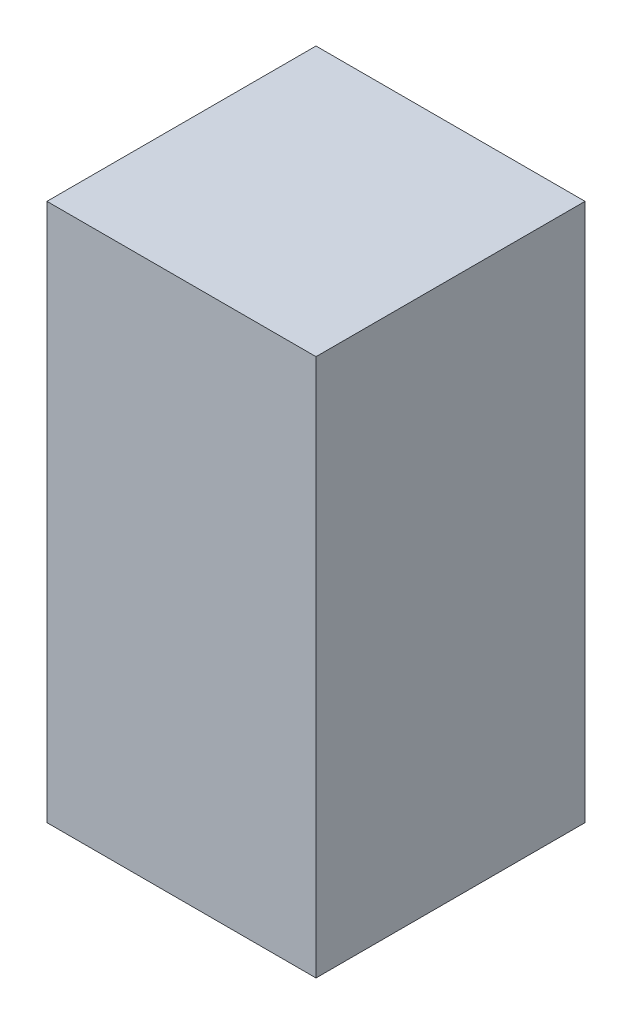
SolidWorks part; units mm, degrees
ref_plane "Front Plane" through (0, 0, 0) normal (0, 0, 1) x (1, 0, 0)
ref_plane "Top Plane" through (0, 0, 0) normal (0, 1, 0) x (1, 0, 0)
ref_plane "Right Plane" through (0, 0, 0) normal (1, 0, 0) x (0, 0, -1)
sketch "Sketch1" plane through (0, 0, 0) normal (0, 1, 0) x (1, 0, 0)
  line L0 (25.4, -25.4) -> (25.4, 25.4) construction
  line L1 (25.4, 25.4) -> (-25.4, 25.4)
  line L2 (25.4, 25.4) -> (25.4, -25.4)
  line L3 (25.4, -25.4) -> (-25.4, -25.4)
  line L4 (-25.4, 25.4) -> (-25.4, -25.4)
  line L5 (25.4, 25.4) -> (-25.4, -25.4) construction
  line L6 (25.4, -25.4) -> (-25.4, 25.4) construction
  line L7 (-25.4, -25.4) -> (25.4, -25.4) construction
  point P0 (0, 0)
extrude "Boss-Extrude1" add sketch "Sketch1" along normal blind 101.6
